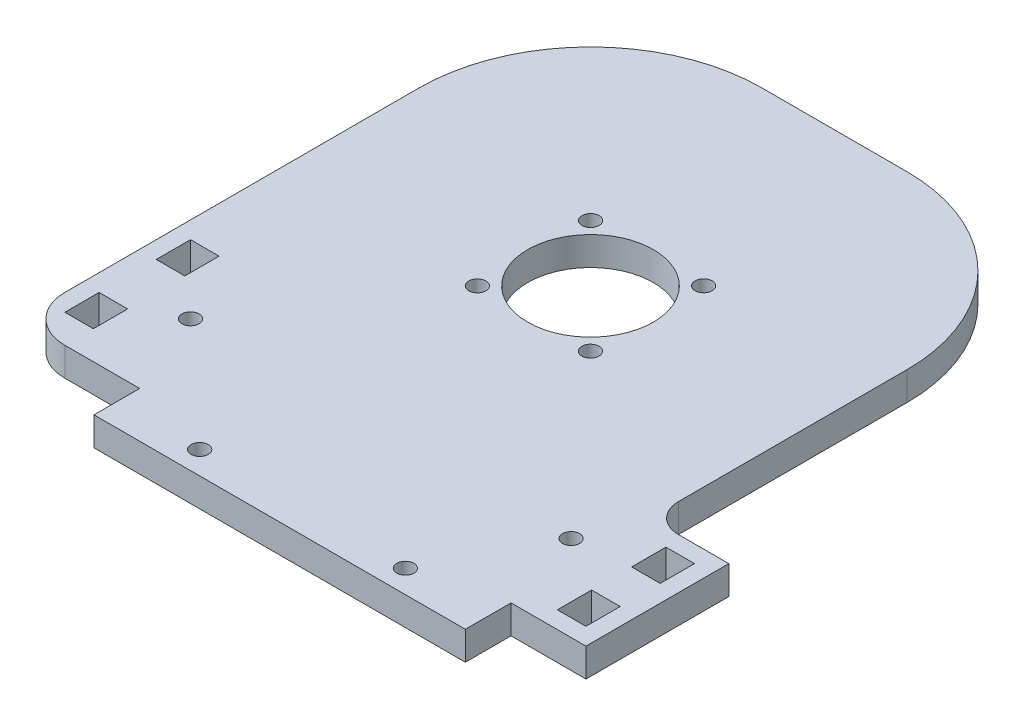
SolidWorks part; units mm, degrees
ref_plane "Front Plane" through (0, 0, 0) normal (0, 0, 1) x (1, 0, 0)
ref_plane "Top Plane" through (0, 0, 0) normal (0, 1, 0) x (1, 0, 0)
ref_plane "Right Plane" through (0, 0, 0) normal (1, 0, 0) x (0, 0, -1)
sketch "Sketch1" plane through (0, 0, 0) normal (0, 1, 0) x (1, 0, 0)
  line L1 (40.394, 14.994) -> (40.394, -25.006)
  line L2 (54.2, -30) -> (54.2, -55)
  line L3 (54.2, -55) -> (41.1, -55)
  line L4 (-45, -47.0008) -> (-45, 15.0011)
  line L7 (-23.9, -55) -> (-23.9, -63)
  line L8 (-23.9, -63) -> (41.1, -63)
  line L9 (41.1, -63) -> (41.1, -55)
  line L10 (-23.9, -55) -> (-37.0004, -55)
  line L11 (45.4, -30) -> (54.2, -30)
  line L12 (-42, -28) -> (-37, -28)
  line L13 (-42, -44) -> (-37, -44)
  line L14 (-42, -44) -> (-42, -50)
  line L15 (-42, -50) -> (-37, -50)
  line L16 (-37, -44) -> (-37, -50)
  line L17 (-39.5, -50) -> (-39.5, -44) construction
  line L18 (-42, -47) -> (-37, -47) construction
  line L19 (-42, -28) -> (-42, -34)
  line L20 (-42, -34) -> (-37, -34)
  line L21 (-37, -28) -> (-37, -34)
  line L22 (-39.5, -34) -> (-39.5, -28) construction
  line L23 (-42, -31) -> (-37, -31) construction
  line L24 (46.2, -33) -> (51.2, -33)
  line L25 (46.2, -46) -> (51.2, -46)
  line L26 (46.2, -46) -> (46.2, -52)
  line L27 (46.2, -52) -> (51.2, -52)
  line L28 (51.2, -46) -> (51.2, -52)
  line L29 (48.7, -52) -> (48.7, -46) construction
  line L30 (46.2, -49) -> (51.2, -49) construction
  line L31 (46.2, -33) -> (46.2, -39)
  line L32 (46.2, -39) -> (51.2, -39)
  line L33 (51.2, -33) -> (51.2, -39)
  line L34 (48.7, -39) -> (48.7, -33) construction
  line L35 (46.2, -36) -> (51.2, -36) construction
  line L36 (-15.0011, 45) -> (10.3972, 44.9972)
  circle A2 centre (0, 0) radius 11
  circle A7 centre (0, 0) radius 14 construction
  circle A14 centre (9.8929, 9.9061) radius 1.5
  circle A15 centre (9.8929, -9.9061) radius 1.5
  circle A16 centre (-9.8929, -9.9061) radius 1.5
  circle A17 centre (-9.8929, 9.9061) radius 1.5
  circle A18 centre (-9.4, -59) radius 1.5
  circle A19 centre (26.6, -59) radius 1.5
  arc A20 (-45, -47.0008) -> (-37.0004, -55) centre (-37.0004, -47.0004) ccw
  arc A21 (-45, 15.0011) -> (-15.0011, 45) centre (-15.0011, 15.0011) cw
  circle A25 centre (-30, -40) radius 1.5
  circle A26 centre (36.6, -40) radius 1.5
  arc A28 (40.394, -25.006) -> (45.4, -30) centre (45.394, -25) ccw
  arc A29 (40.394, 14.994) -> (10.3972, 44.9972) centre (10.394, 14.9972) ccw
  point P48 (-39.5, -31)
  point P65 (48.7, -36)
  point P72 (48.7, -49)
  point P139 (-39.5, -47)
  dimension "D1" = 22
  dimension "D2" = 28
  dimension "D4" = 70.0011
  dimension "D5" = 3
  dimension "D6" = 13.1
  dimension "D9" = 3
  dimension "D7" = 3
  dimension "D8" = 3
  dimension "D25" = 3
  dimension "D26" = 3
  dimension "D27" = 7.9996
  dimension "D28" = 9.8929
  dimension "D30" = 90
  dimension "D31" = 29.9989
  dimension "D34" = 59.7441
  dimension "D10" = 90
  dimension "D60" = 15
  dimension "D62" = 3
  dimension "D65" = 3
  dimension "D33" = 40
  dimension "D41" = 90
  dimension "D42" = 5
  dimension "D13" = 30
  dimension "D11" = 62.002
  dimension "D12" = 21.2148
  dimension "D14" = 25
  dimension "D15" = 21.1
  dimension "D16" = 13.1004
  dimension "D17" = 108
  dimension "D18" = 8
  dimension "D19" = 65
  dimension "D20" = 9.8929
  dimension "D21" = 14.5
  dimension "D22" = 36
  dimension "D23" = 4
  dimension "D24" = 9.9061
  dimension "D29" = 59.8169
  dimension "D32" = 9.9061
  dimension "D35" = 29.994
  dimension "D43" = 8.8
  dimension "D44" = 6
  dimension "D45" = 5
  dimension "D46" = 6
  dimension "D47" = 5
  dimension "D48" = 10
  dimension "D49" = 6
  dimension "D50" = 5
  dimension "D51" = 6
  dimension "D52" = 5
  dimension "D53" = 7
  dimension "D54" = 5
  dimension "D55" = 3
  dimension "D56" = 3
  dimension "D57" = 3
  dimension "D58" = 3
  dimension "D59" = 3
  dimension "D61" = 15
  dimension "D63" = 66.6
  dimension "D64" = 15
extrude "Boss-Extrude1" add sketch "Sketch1" along normal blind 5
